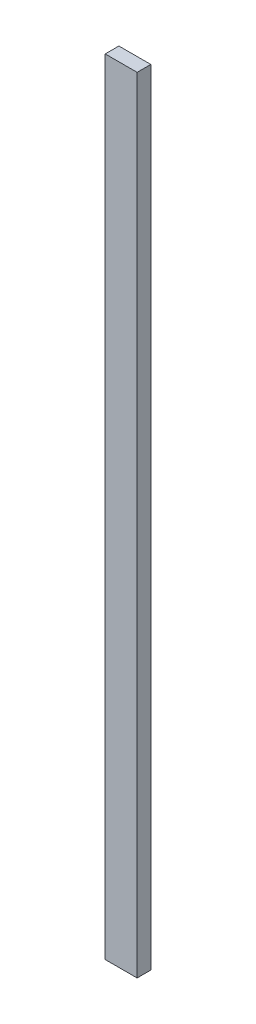
SolidWorks part; units mm, degrees
ref_plane "Front Plane" through (0, 0, 0) normal (0, 0, 1) x (1, 0, 0)
ref_plane "Top Plane" through (0, 0, 0) normal (0, 1, 0) x (1, 0, 0)
ref_plane "Right Plane" through (0, 0, 0) normal (1, 0, 0) x (0, 0, -1)
sketch "Sketch1" plane through (0, 0, 0) normal (0, 1, 0) x (1, 0, 0)
  line L1 (-44.45, -19.05) -> (44.45, -19.05)
  line L2 (-44.45, -19.05) -> (-44.45, 19.05)
  line L3 (-44.45, 19.05) -> (44.45, 19.05)
  line L4 (44.45, -19.05) -> (44.45, 19.05)
  line L5 (-44.45, -19.05) -> (44.45, 19.05) construction
  line L6 (-44.45, 19.05) -> (44.45, -19.05) construction
  point P0 (0, 0)
  dimension "D1" = 88.9
  dimension "D2" = 38.1
extrude "Boss-Extrude1" add sketch "Sketch1" along normal blind 2184.4
